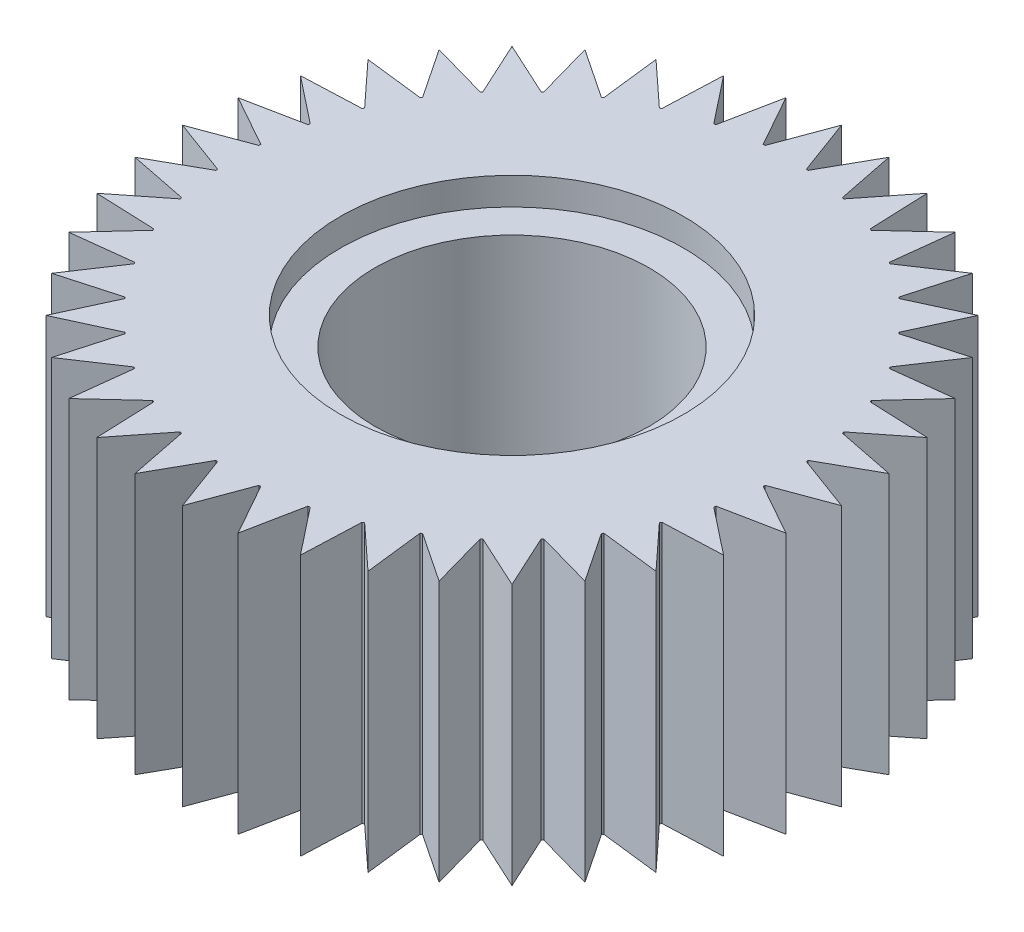
SolidWorks part; units mm, degrees
ref_plane "Alzado" through (0, 0, 0) normal (0, 0, 1) x (1, 0, 0)
ref_plane "Planta" through (0, 0, 0) normal (0, 1, 0) x (1, 0, 0)
ref_plane "Vista lateral" through (0, 0, 0) normal (1, 0, 0) x (0, 0, -1)
sketch "Croquis1" plane through (0, 0, 0) normal (0, 1, 0) x (1, 0, 0)
  circle A0 centre (0, 0) radius 3
  circle A1 centre (0, 0) radius 10
  dimension "D1" = 6
  dimension "D2" = 20
extrude "Saliente-Extruir1" add sketch "Croquis1" along normal blind 19
sketch "Croquis2" plane through (0, 19, 0) normal (0, 1, 0) x (1, 0, 0)
  line L0 (0, -24) -> (1.5, -19.9437)
  line L1 (0, -39) -> (0, -32.1886) construction
  line L2 (0, -24) -> (-1.5, -19.9437)
  line L3 (-3.7544, -23.7045) -> (-4.6014, -19.4635)
  line L4 (-3.7544, -23.7045) -> (-1.6383, -19.9328)
  line L5 (-7.4164, -22.8254) -> (-7.5895, -18.504)
  line L6 (-7.4164, -22.8254) -> (-4.7363, -19.4311)
  line L7 (-10.8958, -21.3842) -> (-10.3907, -17.089)
  line L8 (-10.8958, -21.3842) -> (-7.7177, -18.4509)
  line L9 (-14.1068, -19.4164) -> (-12.9361, -15.2531)
  line L10 (-14.1068, -19.4164) -> (-10.5091, -17.0164)
  line L11 (-16.9706, -16.9706) -> (-15.163, -13.0416)
  line L12 (-16.9706, -16.9706) -> (-13.0416, -15.163)
  line L13 (-19.4164, -14.1068) -> (-17.0164, -10.5091)
  line L14 (-19.4164, -14.1068) -> (-15.2531, -12.9361)
  line L15 (-21.3842, -10.8958) -> (-18.4509, -7.7177)
  line L16 (-21.3842, -10.8958) -> (-17.089, -10.3907)
  line L17 (-22.8254, -7.4164) -> (-19.4311, -4.7363)
  line L18 (-22.8254, -7.4164) -> (-18.504, -7.5895)
  line L19 (-23.7045, -3.7544) -> (-19.9328, -1.6383)
  line L20 (-23.7045, -3.7544) -> (-19.4635, -4.6014)
  line L21 (-24, 0) -> (-19.9437, 1.5)
  line L22 (-24, 0) -> (-19.9437, -1.5)
  line L23 (-23.7045, 3.7544) -> (-19.4635, 4.6014)
  line L24 (-23.7045, 3.7544) -> (-19.9328, 1.6383)
  line L25 (-22.8254, 7.4164) -> (-18.504, 7.5895)
  line L26 (-22.8254, 7.4164) -> (-19.4311, 4.7363)
  line L27 (-21.3842, 10.8958) -> (-17.089, 10.3907)
  line L28 (-21.3842, 10.8958) -> (-18.4509, 7.7177)
  line L29 (-19.4164, 14.1068) -> (-15.2531, 12.9361)
  line L30 (-19.4164, 14.1068) -> (-17.0164, 10.5091)
  line L31 (-16.9706, 16.9706) -> (-13.0416, 15.163)
  line L32 (-16.9706, 16.9706) -> (-15.163, 13.0416)
  line L33 (-14.1068, 19.4164) -> (-10.5091, 17.0164)
  line L34 (-14.1068, 19.4164) -> (-12.9361, 15.2531)
  line L35 (-10.8958, 21.3842) -> (-7.7177, 18.4509)
  line L36 (-10.8958, 21.3842) -> (-10.3907, 17.089)
  line L37 (-7.4164, 22.8254) -> (-4.7363, 19.4311)
  line L38 (-7.4164, 22.8254) -> (-7.5895, 18.504)
  line L39 (-3.7544, 23.7045) -> (-1.6383, 19.9328)
  line L40 (-3.7544, 23.7045) -> (-4.6014, 19.4635)
  line L41 (0, 24) -> (1.5, 19.9437)
  line L42 (0, 24) -> (-1.5, 19.9437)
  line L43 (3.7544, 23.7045) -> (4.6014, 19.4635)
  line L44 (3.7544, 23.7045) -> (1.6383, 19.9328)
  line L45 (7.4164, 22.8254) -> (7.5895, 18.504)
  line L46 (7.4164, 22.8254) -> (4.7363, 19.4311)
  line L47 (10.8958, 21.3842) -> (10.3907, 17.089)
  line L48 (10.8958, 21.3842) -> (7.7177, 18.4509)
  line L49 (14.1068, 19.4164) -> (12.9361, 15.2531)
  line L50 (14.1068, 19.4164) -> (10.5091, 17.0164)
  line L51 (16.9706, 16.9706) -> (15.163, 13.0416)
  line L52 (16.9706, 16.9706) -> (13.0416, 15.163)
  line L53 (19.4164, 14.1068) -> (17.0164, 10.5091)
  line L54 (19.4164, 14.1068) -> (15.2531, 12.9361)
  line L55 (21.3842, 10.8958) -> (18.4509, 7.7177)
  line L56 (21.3842, 10.8958) -> (17.089, 10.3907)
  line L57 (22.8254, 7.4164) -> (19.4311, 4.7363)
  line L58 (22.8254, 7.4164) -> (18.504, 7.5895)
  line L59 (23.7045, 3.7544) -> (19.9328, 1.6383)
  line L60 (23.7045, 3.7544) -> (19.4635, 4.6014)
  line L61 (24, 0) -> (19.9437, -1.5)
  line L62 (24, 0) -> (19.9437, 1.5)
  line L63 (23.7045, -3.7544) -> (19.4635, -4.6014)
  line L64 (23.7045, -3.7544) -> (19.9328, -1.6383)
  line L65 (22.8254, -7.4164) -> (18.504, -7.5895)
  line L66 (22.8254, -7.4164) -> (19.4311, -4.7363)
  line L67 (21.3842, -10.8958) -> (17.089, -10.3907)
  line L68 (21.3842, -10.8958) -> (18.4509, -7.7177)
  line L69 (19.4164, -14.1068) -> (15.2531, -12.9361)
  line L70 (19.4164, -14.1068) -> (17.0164, -10.5091)
  line L71 (16.9706, -16.9706) -> (13.0416, -15.163)
  line L72 (16.9706, -16.9706) -> (15.163, -13.0416)
  line L73 (14.1068, -19.4164) -> (10.5091, -17.0164)
  line L74 (14.1068, -19.4164) -> (12.9361, -15.2531)
  line L75 (10.8958, -21.3842) -> (7.7177, -18.4509)
  line L76 (10.8958, -21.3842) -> (10.3907, -17.089)
  line L77 (7.4164, -22.8254) -> (4.7363, -19.4311)
  line L78 (7.4164, -22.8254) -> (7.5895, -18.504)
  line L79 (3.7544, -23.7045) -> (1.6383, -19.9328)
  line L80 (3.7544, -23.7045) -> (4.6014, -19.4635)
  circle A0 centre (0, 0) radius 20
  circle A1 centre (0, 0) radius 24
  circle A2 centre (0, 0) radius 10
  circle A3 centre (0, 0) radius 10 construction
  point P190 (0, 0)
  circle M1 centre (0, 0) radius 10
  dimension "D1" = 40
  dimension "D2" = 4
  dimension "D3" = 1.5
  dimension "D4" = 1.5
  dimension "D5" = 40
extrude "Saliente-Extruir2" add sketch "Croquis2" against normal blind 19 contours L1 A0 M1 | A0 L1 A2 | A0 L79 L80 | A0 L77 L78 | A0 L75 L76 | A0 L73 L74 | A0 L71 L72 | A0 L69 L70 | A0 L67 L68 | L1 L0 A0 | L2 L1 A0 | A0 L3 L4 | A0 L65 L66 | A0 L63 L64 | A0 L61 L62 | A0 L59 L60 | A0 L57 L58 | A0 L55 L56 | A0 L53 L54 | A0 L51 L52 | A0 L49 L50 | A0 L47 L48 | A0 L45 L46 | A0 L43 L44 | L1 A0 L41 | A0 L1 L42 | A0 L39 L40 | A0 L37 L38 | A0 L35 L36 | A0 L33 L34 | A0 L31 L32 | A0 L29 L30 | A0 L27 L28 | A0 L25 L26 | A0 L23 L24 | A0 L21 L22 | A0 L19 L20 | A0 L17 L18 | A0 L15 L16 | A0 L13 L14 | A0 L11 L12 | A0 L9 L10 | A0 L7 L8 | A0 L5 L6
sketch "Croquis3" plane through (0, 0, 0) normal (0, -1, 0) x (1, 0, 0)
  circle A0 centre (0, 0) radius 10
  dimension "D1" = 20
extrude "Cortar-Extruir1" cut sketch "Croquis3" against normal through all
sketch "Croquis4" plane through (0, 19, 0) normal (0, 1, 0) x (1, 0, 0)
  circle A0 centre (0, 0) radius 12.5
  dimension "D1" = 25
extrude "Cortar-Extruir2" cut sketch "Croquis4" against normal blind 2
sketch "Croquis5" plane through (0, 0, 0) normal (0, -1, 0) x (1, 0, 0)
  circle A0 centre (0, 0) radius 12.5
  dimension "D1" = 25
extrude "Cortar-Extruir3" cut sketch "Croquis5" against normal blind 2
